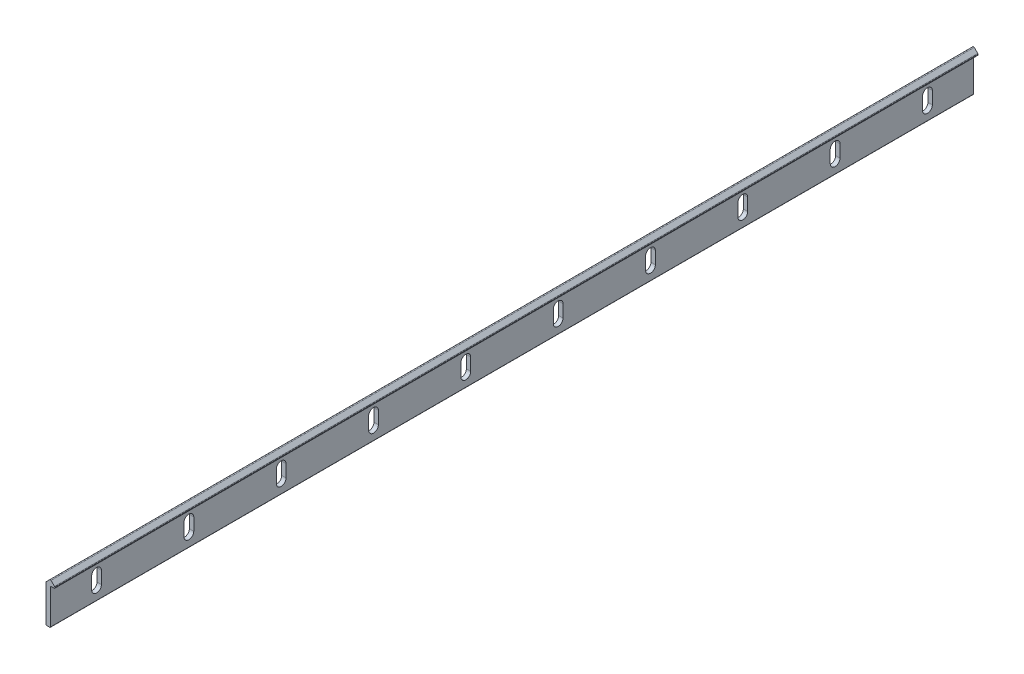
SolidWorks part; units mm, degrees
material "6061-T6 (SS)"
ref_plane "Front Plane" through (0, 0, 0) normal (0, 0, 1) x (1, 0, 0)
ref_plane "Top Plane" through (0, 0, 0) normal (0, 1, 0) x (1, 0, 0)
ref_plane "Right Plane" through (0, 0, 0) normal (1, 0, 0) x (0, 0, -1)
sketch "Sketch1" plane through (0, 0, 0) normal (0, 0, 1) x (1, 0, 0)
  line L0 (0, 20.3302) -> (2.0196, 22.3498)
  line L1 (0, 0) -> (2.375, 0)
  line L2 (0, 20.3302) -> (0, 0)
  line L4 (2.375, 0) -> (2.375, 19.5291)
  line L5 (2.375, 19.5291) -> (4.75, 19.5291)
  line L7 (2.7304, 22.3498) -> (4.75, 20.3302)
  line L8 (4.75, 19.5291) -> (4.75, 20.3302)
  arc A0 (2.7304, 22.3498) -> (2.0196, 22.3498) centre (2.375, 21.9944) ccw
  point P9 (2.375, 22.7052)
  dimension "D5" = 0.5026
  dimension "D6" = 22.497
  dimension "D1" = 2.375
  dimension "D2" = 19.5291
  dimension "D3" = 2.375
  dimension "D4" = 2.9679
extrude "Boss-Extrude1" add sketch "Sketch1" along normal blind 500
fillet "Fillet1" radius 0.5033 1 edges at (0, 20.3302, 250)
fillet "Fillet2" radius 0.504 1 edges at (4.75, 20.3302, 250)
fillet "Fillet3" radius 0.3016 1 edges at (4.75, 19.5291, 250)
fillet "Fillet4" radius 0.3016 2 edges at (0, 0, 250) (2.375, 0, 250)
sketch "Sketch2" plane through (0, 0, 0) normal (-1, 0, 0) x (0, 0, 1)
  line L0 (25, 13.1043) -> (25, 6.4043) construction
  line L1 (27.65, 13.1043) -> (27.65, 6.4043)
  line L2 (22.35, 13.1043) -> (22.35, 6.4043)
  line L3 (500, 0) -> (0, 0) construction
  line L4 (0, 20.1217) -> (0, 0.3016) construction
  arc A0 (27.65, 13.1043) -> (22.35, 13.1043) centre (25, 13.1043) ccw
  arc A1 (22.35, 6.4043) -> (27.65, 6.4043) centre (25, 6.4043) ccw
  point P2 (25, 9.7543)
  dimension "D3" = 9.7543
  dimension "D1" = 5.3
  dimension "D2" = 6.7
  dimension "D4" = 25
extrude "Cut-Extrude1" cut sketch "Sketch2" against normal up to next (2.375 mm away)
pattern_linear "LPattern1" count 10 spacing 50 along (0, 0, 1) of "Cut-Extrude1"
equation "\"D3@Sketch1\"=\"D1@Sketch1\""
